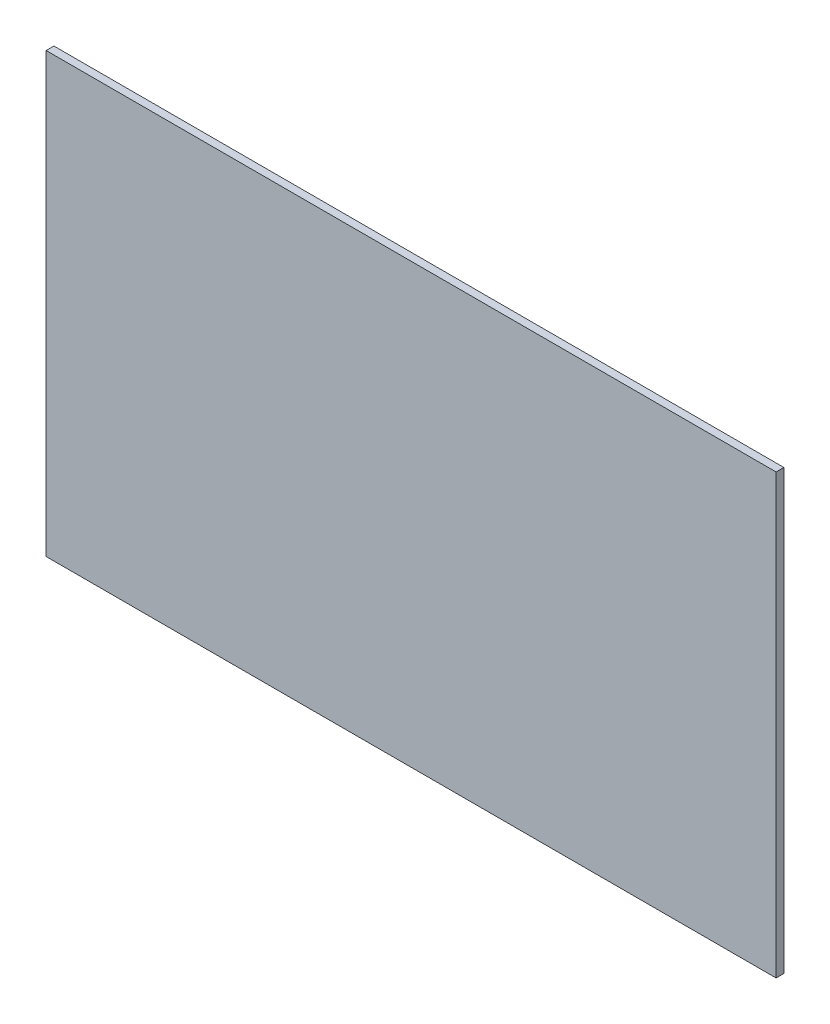
SolidWorks part; units mm, degrees
ref_plane "Plan de face" through (0, 0, 0) normal (0, 0, 1) x (1, 0, 0)
ref_plane "Plan de dessus" through (0, 0, 0) normal (0, 1, 0) x (1, 0, 0)
ref_plane "Plan de droite" through (0, 0, 0) normal (1, 0, 0) x (0, 0, -1)
sketch "Esquisse1" plane through (0, 0, 0) normal (0, 0, 1) x (1, 0, 0)
  line L1 (-563, 338) -> (563, 338)
  line L2 (-563, 338) -> (-563, -338)
  line L3 (-563, -338) -> (563, -338)
  line L4 (563, 338) -> (563, -338)
  line L5 (-563, 338) -> (563, -338) construction
  line L6 (-563, -338) -> (563, 338) construction
  point P0 (0, 0)
  dimension "D1" = 1126
  dimension "D2" = 676
extrude "Boss.-Extru.1" add sketch "Esquisse1" along normal blind 12
